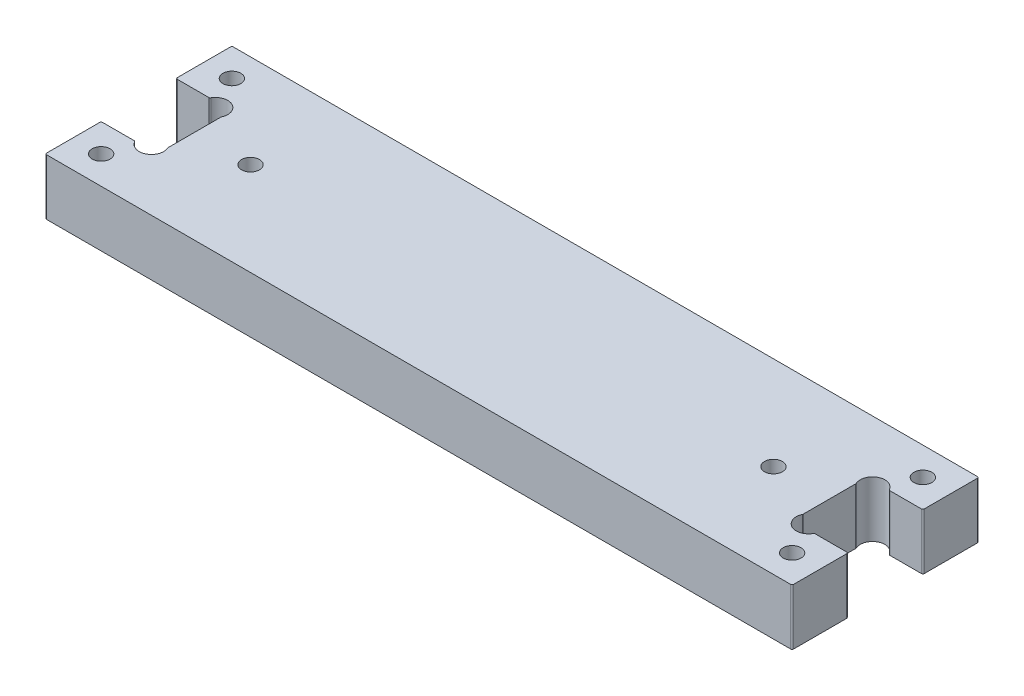
SolidWorks part; units mm, degrees
material "PE High Density"
ref_plane "Front Plane" through (0, 0, 0) normal (0, 0, 1) x (1, 0, 0)
ref_plane "Top Plane" through (0, 0, 0) normal (0, 1, 0) x (1, 0, 0)
ref_plane "Right Plane" through (0, 0, 0) normal (1, 0, 0) x (0, 0, -1)
other "Bounding Box"
ref_plane "Default Plane" through (13.8565, 3.175, 6.7999) normal (0, -1, 0) x (-1, 0, 0)
sketch "Sketch1" plane through (0, 0, 0) normal (0, 1, 0) x (1, 0, 0)
  line L1 (-53.975, -12.7) -> (53.975, -12.7)
  line L2 (-53.975, -12.7) -> (-53.975, 12.7)
  line L3 (-53.975, 12.7) -> (53.975, 12.7)
  line L4 (53.975, -12.7) -> (53.975, 12.7)
  line L5 (-53.975, -12.7) -> (53.975, 12.7) construction
  line L6 (-53.975, 12.7) -> (53.975, -12.7) construction
  point P0 (0, 0)
  dimension "D1" = 107.95
  dimension "D2" = 25.4
extrude "Boss-Extrude1" add sketch "Sketch1" along normal blind 9.525
sketch "Sketch2" [suppressed] plane through (0, 0, 0) normal (0, -1, 0) x (-1, 0, 0)
  line L0 (53.975, -12.7) -> (-53.975, -12.7) construction
  line L1 (41.3004, -12.7) -> (31.7246, -12.7)
  line L2 (41.3004, -12.7) -> (41.3004, -3.048)
  line L3 (41.3004, -3.048) -> (31.7246, -3.048)
  line L4 (31.7246, -12.7) -> (31.7246, -3.048)
  line L5 (41.3004, -12.7) -> (31.7246, -3.048) construction
  line L6 (41.3004, -3.048) -> (31.7246, -12.7) construction
  line L7 (53.975, -12.7) -> (36.5125, -12.7) construction
  line L8 (19.0754, -12.7) -> (9.4996, -12.7)
  line L9 (19.0754, -12.7) -> (19.0754, 0.0508)
  line L10 (19.0754, 0.0508) -> (9.4996, 0.0508)
  line L11 (9.4996, -12.7) -> (9.4996, 0.0508)
  line L12 (19.0754, -12.7) -> (9.4996, 0.0508) construction
  line L13 (19.0754, 0.0508) -> (9.4996, -12.7) construction
  line L14 (-9.4996, -12.7) -> (-19.0754, -12.7)
  line L15 (-9.4996, -12.7) -> (-9.4996, 0.0508)
  line L16 (-9.4996, 0.0508) -> (-19.0754, 0.0508)
  line L17 (-19.0754, -12.7) -> (-19.0754, 0.0508)
  line L18 (-9.4996, -12.7) -> (-19.0754, 0.0508) construction
  line L19 (-9.4996, 0.0508) -> (-19.0754, -12.7) construction
  line L20 (-31.7246, -12.7) -> (-41.3004, -12.7)
  line L21 (-31.7246, -12.7) -> (-31.7246, -3.048)
  line L22 (-31.7246, -3.048) -> (-41.3004, -3.048)
  line L23 (-41.3004, -12.7) -> (-41.3004, -3.048)
  line L24 (-31.7246, -12.7) -> (-41.3004, -3.048) construction
  line L25 (-31.7246, -3.048) -> (-41.3004, -12.7) construction
  line L26 (9.4996, 0.0508) -> (-9.4996, 0.0508) construction
  line L27 (36.5125, -12.7) -> (14.2875, -12.7) construction
  line L28 (41.3004, -3.048) -> (53.975, -3.048) construction
  line L29 (-53.975, -12.7) -> (-53.975, 12.7) construction
  line L30 (53.975, 12.7) -> (53.975, -12.7) construction
  line L31 (-41.3004, -3.048) -> (-53.975, -3.048) construction
  line L32 (14.2875, -12.7) -> (-14.2875, -12.7) construction
  line L33 (-14.2875, -12.7) -> (-36.5125, -12.7) construction
  line L34 (-36.5125, -12.7) -> (-53.975, -12.7) construction
  point P4 (36.5125, -7.874)
  point P11 (14.2875, -6.3246)
  point P16 (-14.2875, -6.3246)
  point P21 (-36.5125, -7.874)
  point P38 (0, 0.0508)
  dimension "D1" = 28.575
  dimension "D2" = 9.5758
  dimension "D3" = 17.4625
  dimension "D4" = 9.652
  dimension "D5" = 12.7508
extrude "Cut-Extrude1" [suppressed] cut sketch "Sketch2" against normal through all
sketch "Sketch3" plane through (0, 0, 0) normal (0, -1, 0) x (1, 0, 0)
  line L0 (53.975, 12.7) -> (53.975, -12.7) construction
  line L1 (-53.975, 12.7) -> (53.975, 12.7)
  line L2 (-53.975, 12.7) -> (-53.975, 6.35)
  line L3 (-53.975, 6.35) -> (53.975, 6.35)
  line L4 (53.975, 12.7) -> (53.975, 6.35)
  line L5 (-53.975, 12.7) -> (53.975, 6.35) construction
  line L6 (-53.975, 6.35) -> (53.975, 12.7) construction
  point P4 (0, 9.525)
  dimension "D1" = 6.35
extrude "Cut-Extrude2" cut sketch "Sketch3" against normal through all
sketch "Sketch4" [suppressed] plane through (0, 0, 0) normal (0, -1, 0) x (1, 0, 0)
  line L0 (-39.4716, 3.048) -> (-40.386, 4.9335) construction
  line L1 (-41.3004, 3.048) -> (-31.7246, 3.048) construction
  line L2 (-19.0754, -0.0508) -> (-18.161, 1.8347) construction
  line L3 (-40.386, 4.9335) -> (-32.639, 4.9335) construction
  line L4 (-41.3004, 3.048) -> (-40.386, 4.9335) construction
  line L5 (-33.5534, 3.048) -> (-32.639, 4.9335) construction
  line L6 (-32.639, 4.9335) -> (-31.7246, 3.048) construction
  line L7 (-18.161, 1.8347) -> (-17.2466, -0.0508) construction
  line L8 (-19.0754, -0.0508) -> (-9.4996, -0.0508) construction
  line L9 (-11.3284, -0.0508) -> (-10.414, 1.8347) construction
  line L10 (-10.414, 1.8347) -> (-9.4996, -0.0508) construction
  line L11 (9.4996, -0.0508) -> (10.414, 1.8347) construction
  line L12 (10.414, 1.8347) -> (11.3284, -0.0508) construction
  line L13 (17.2466, -0.0508) -> (18.161, 1.8347) construction
  line L14 (18.161, 1.8347) -> (19.0754, -0.0508) construction
  line L15 (9.4996, -0.0508) -> (19.0754, -0.0508) construction
  line L16 (-18.161, 1.8347) -> (-10.414, 1.8347) construction
  line L17 (31.7246, 3.048) -> (32.639, 4.9335) construction
  line L18 (32.639, 4.9335) -> (33.5534, 3.048) construction
  line L19 (39.4716, 3.048) -> (40.386, 4.9335) construction
  line L20 (40.386, 4.9335) -> (41.3004, 3.048) construction
  line L21 (31.7246, 3.048) -> (41.3004, 3.048) construction
  line L22 (10.414, 1.8347) -> (18.161, 1.8347) construction
  line L23 (32.639, 4.9335) -> (40.386, 4.9335) construction
  circle A1 centre (-40.386, 4.9335) radius 2.0955
  circle A2 centre (-32.639, 4.9335) radius 2.0955
  circle A3 centre (-18.161, 1.8347) radius 2.0955
  circle A4 centre (-10.414, 1.8347) radius 2.0955
  circle A5 centre (10.414, 1.8347) radius 2.0955
  circle A6 centre (18.161, 1.8347) radius 2.0955
  circle A7 centre (32.639, 4.9335) radius 2.0955
  circle A8 centre (40.386, 4.9335) radius 2.0955
  dimension "D1" = 1.8288
  dimension "D2" = 4.191
extrude "Cut-Extrude3" [suppressed] cut sketch "Sketch4" against normal through all
fillet "Fillet1" [suppressed] radius 0.635
sketch "Sketch5" plane through (0, 9.525, 0) normal (0, 1, 0) x (1, 0, 0)
  line L0 (53.975, 3.175) -> (44.45, 3.175) construction
  line L1 (53.975, -6.35) -> (53.975, 12.7) construction
  line L2 (44.45, 3.175) -> (44.45, -6.35) construction
  line L3 (-53.975, -6.35) -> (53.975, -6.35) construction
  line L4 (44.45, 3.175) -> (44.45, 12.7) construction
  line L5 (53.975, 12.7) -> (-53.975, 12.7) construction
  line L6 (0, 0) -> (0, -6.35) construction
  circle A0 centre (44.45, 3.175) radius 1.524
  circle A2 centre (-44.45, 3.175) radius 1.524
  dimension "D2" = 3.048
  dimension "D1" = 9.525
extrude "Cut-Extrude4" cut sketch "Sketch5" against normal through all
sketch "Sketch6" plane through (0, 9.525, 0) normal (0, 1, 0) x (1, 0, 0)
  line L0 (53.975, -6.35) -> (53.975, 12.7) construction
  line L1 (-53.975, 12.7) -> (53.975, 12.7)
  line L2 (-53.975, 12.7) -> (-53.975, 19.05)
  line L3 (-53.975, 19.05) -> (53.975, 19.05)
  line L4 (53.975, 12.7) -> (53.975, 19.05)
  line L5 (-53.975, -6.35) -> (53.975, -6.35)
  line L6 (-53.975, -6.35) -> (-53.975, -12.7)
  line L7 (-53.975, -12.7) -> (53.975, -12.7)
  line L8 (53.975, -6.35) -> (53.975, -12.7)
  dimension "D1" = 6.35
extrude "Boss-Extrude2" add sketch "Sketch6" against normal through all
sketch "Sketch7" plane through (0, 9.525, 0) normal (0, 1, 0) x (1, 0, 0)
  line L1 (53.975, 19.05) -> (63.5, 19.05)
  line L2 (53.975, 19.05) -> (53.975, 9.525)
  line L3 (53.975, 9.525) -> (63.5, 9.525)
  line L4 (63.5, 19.05) -> (63.5, 9.525)
  line L5 (53.975, 19.05) -> (63.5, 9.525) construction
  line L6 (53.975, 9.525) -> (63.5, 19.05) construction
  line L7 (53.975, -12.7) -> (63.5, -12.7)
  line L8 (53.975, -12.7) -> (53.975, -3.175)
  line L9 (53.975, -3.175) -> (63.5, -3.175)
  line L10 (63.5, -12.7) -> (63.5, -3.175)
  line L11 (53.975, -12.7) -> (63.5, -3.175) construction
  line L12 (53.975, -3.175) -> (63.5, -12.7) construction
  line L13 (-53.975, -12.7) -> (-63.5, -12.7)
  line L14 (-53.975, -12.7) -> (-53.975, -3.175)
  line L15 (-53.975, -3.175) -> (-63.5, -3.175)
  line L16 (-63.5, -12.7) -> (-63.5, -3.175)
  line L17 (-53.975, -12.7) -> (-63.5, -3.175) construction
  line L18 (-53.975, -3.175) -> (-63.5, -12.7) construction
  line L19 (-53.975, 19.05) -> (-63.5, 19.05)
  line L20 (-53.975, 19.05) -> (-53.975, 9.525)
  line L21 (-53.975, 9.525) -> (-63.5, 9.525)
  line L22 (-63.5, 19.05) -> (-63.5, 9.525)
  line L23 (-53.975, 19.05) -> (-63.5, 9.525) construction
  line L24 (-53.975, 9.525) -> (-63.5, 19.05) construction
  circle A0 centre (-58.7375, 14.2875) radius 1.524
  circle A1 centre (-58.7375, -7.9375) radius 1.524
  circle A2 centre (58.7375, -7.9375) radius 1.524
  circle A3 centre (58.7375, 14.2875) radius 1.524
  circle A4 centre (-44.45, 3.175) radius 1.524 construction
  point P4 (58.7375, 14.2875)
  point P10 (58.7375, -7.9375)
  point P16 (-58.7375, -7.9375)
  point P22 (-58.7375, 14.2875)
  dimension "D1" = 9.525
  dimension "D2" = 12.7
extrude "Boss-Extrude3" add sketch "Sketch7" against normal through all
sketch "Sketch8" plane through (0, 0, 0) normal (0, -1, 0) x (-1, 0, 0)
  line L0 (53.975, -3.175) -> (55.8605, -2.2606) construction
  line L1 (55.8605, -2.2606) -> (53.975, -1.3462) construction
  line L2 (53.975, 9.525) -> (53.975, -3.175) construction
  line L3 (53.975, 9.525) -> (55.8605, 8.6106) construction
  line L4 (55.8605, 8.6106) -> (53.975, 7.6962) construction
  line L5 (53.975, 7.6962) -> (53.975, 9.525) construction
  line L6 (53.975, -1.3462) -> (53.975, -3.175) construction
  circle A0 centre (55.8605, -2.2606) radius 2.0955
  circle A1 centre (55.8605, 8.6106) radius 2.0955
  dimension "D2" = 4.191
  dimension "D1" = 1.8288
extrude "Cut-Extrude5" cut sketch "Sketch8" against normal through all
mirror "Mirror1" about plane through (0, 0, 0) normal (1, 0, 0) of "Cut-Extrude5"
sketch "Sketch9" [suppressed] plane through (0, 0, 0) normal (0, -1, 0) x (1, 0, 0)
  line L0 (53.975, -12.7) -> (-53.975, -12.7) construction
  line L1 (-53.975, 12.7) -> (-63.5, 12.7)
  line L2 (-53.975, 12.7) -> (-53.975, -12.7)
  line L3 (-53.975, -12.7) -> (-63.5, -12.7)
  line L4 (-63.5, 12.7) -> (-63.5, -12.7)
  line L5 (-53.975, 12.7) -> (-63.5, -12.7) construction
  line L6 (-53.975, -12.7) -> (-63.5, 12.7) construction
  line L7 (53.975, 12.7) -> (63.5, 12.7)
  line L8 (53.975, 12.7) -> (53.975, -12.7)
  line L9 (53.975, -12.7) -> (63.5, -12.7)
  line L10 (63.5, 12.7) -> (63.5, -12.7)
  line L11 (53.975, 12.7) -> (63.5, -12.7) construction
  line L12 (53.975, -12.7) -> (63.5, 12.7) construction
  line L13 (58.7375, -7.9375) -> (58.7375, 0) construction
  line L14 (58.7375, 0) -> (58.7375, 7.9375) construction
  line L15 (-58.7375, 7.9375) -> (-58.7375, 0) construction
  line L16 (-58.7375, 0) -> (-58.7375, -7.9375) construction
  line L17 (-63.5, 7.9375) -> (-58.7375, 7.9375) construction
  line L18 (-58.7375, 7.9375) -> (-58.7375, 12.7) construction
  circle A0 centre (-58.7375, 7.9375) radius 1.524
  circle A1 centre (-58.7375, -7.9375) radius 1.524
  circle A2 centre (58.7375, -7.9375) radius 1.524
  circle A3 centre (58.7375, 7.9375) radius 1.524
  point P4 (-58.7375, 0)
  point P10 (58.7375, 0)
  dimension "D2" = 3.048
  dimension "D1" = 9.525
extrude "Boss-Extrude4" [suppressed] add sketch "Sketch9" against normal through all
sketch "Sketch10" [suppressed] plane through (0, 9.525, 0) normal (0, 1, 0) x (1, 0, 0)
  circle A0 centre (-58.7375, 14.2875) radius 1.905
  circle A1 centre (-58.7375, -7.9375) radius 1.905
  circle A2 centre (58.7375, -7.9375) radius 1.905
  circle A3 centre (58.7375, 14.2875) radius 1.905
  circle A4 centre (-44.45, 3.175) radius 1.7272
  circle A5 centre (44.45, 3.175) radius 1.7272
  dimension "D1" = 3.81
  dimension "D2" = 3.4544
extrude "Cut-Extrude6" [suppressed] cut sketch "Sketch10" against normal through all
fillet "Fillet2" [suppressed] radius 0.254
fillet "Fillet3" radius 0.254 16 edges at (63.5, 4.7625, 12.7) (63.5, 4.7625, 3.175) (63.5, 4.7625, -9.525) (63.5, 4.7625, -19.05) (-63.5, 4.7625, -19.05) (-63.5, 4.7625, -9.525) (-63.5, 4.7625, 3.175) (-63.5, 4.7625, 12.7) (-57.7459, 4.7625, -9.525) (-57.7459, 4.7625, 3.175) (-53.975, 4.7625, -7.6962) (-53.975, 4.7625, 1.3462) (57.7459, 4.7625, -9.525) (53.975, 4.7625, -7.6962) (53.975, 4.7625, 1.3462) (57.7459, 4.7625, 3.175)
